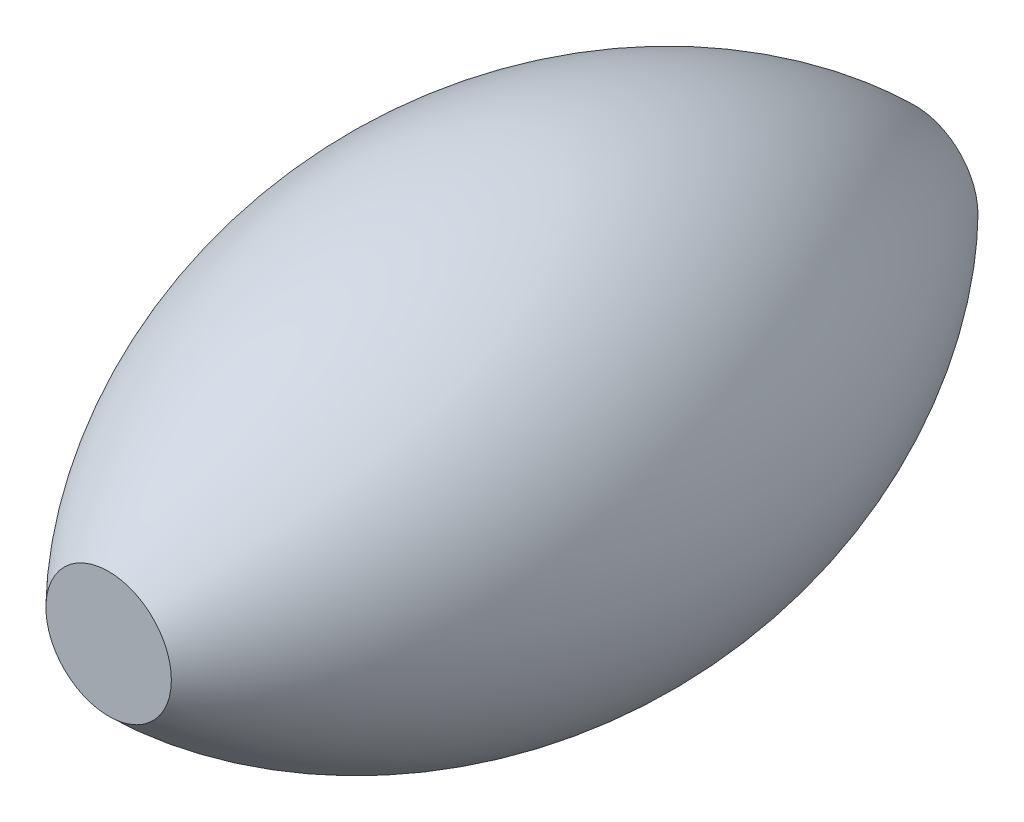
SolidWorks part; units mm, degrees
ref_plane "Front Plane" through (0, 0, 0) normal (0, 0, 1) x (1, 0, 0)
ref_plane "Top Plane" through (0, 0, 0) normal (0, 1, 0) x (1, 0, 0)
ref_plane "Right Plane" through (0, 0, 0) normal (1, 0, 0) x (0, 0, -1)
sketch "Sketch1" plane through (0, 0, 0) normal (1, 0, 0) x (0, 0, -1)
  line L0 (-112.5, 17.5) -> (112.5, 17.5) construction
  line L1 (-112.5, 63.5) -> (112.5, 63.5) construction
  line L2 (-112.5, 63.5) -> (-112.5, -63.5) construction
  line L3 (-112.5, -63.5) -> (112.5, -63.5) construction
  line L4 (112.5, 63.5) -> (112.5, -63.5) construction
  line L5 (-112.5, 63.5) -> (112.5, -63.5) construction
  line L6 (-112.5, -63.5) -> (112.5, 63.5) construction
  line L7 (-112.5, -17.5) -> (112.5, -17.5) construction
  line L8 (0, 17.5) -> (0, -17.5) construction
  line L9 (-112.5, 0) -> (112.5, 0) construction
  line L12 (-112.5, 17.5) -> (-112.5, 0)
  line L13 (-112.5, 0) -> (112.5, 0)
  line L14 (112.5, 0) -> (112.5, 17.5)
  arc A0 (-112.5, 17.5) -> (112.5, 17.5) centre (0, -97.0679) cw
  point P0 (0, 0)
  point P12 (0, 0)
  dimension "D1" = 127
  dimension "D2" = 225
  dimension "D3" = 35
revolve "Revolve1" add sketch "Sketch1" angle 360 about L13
